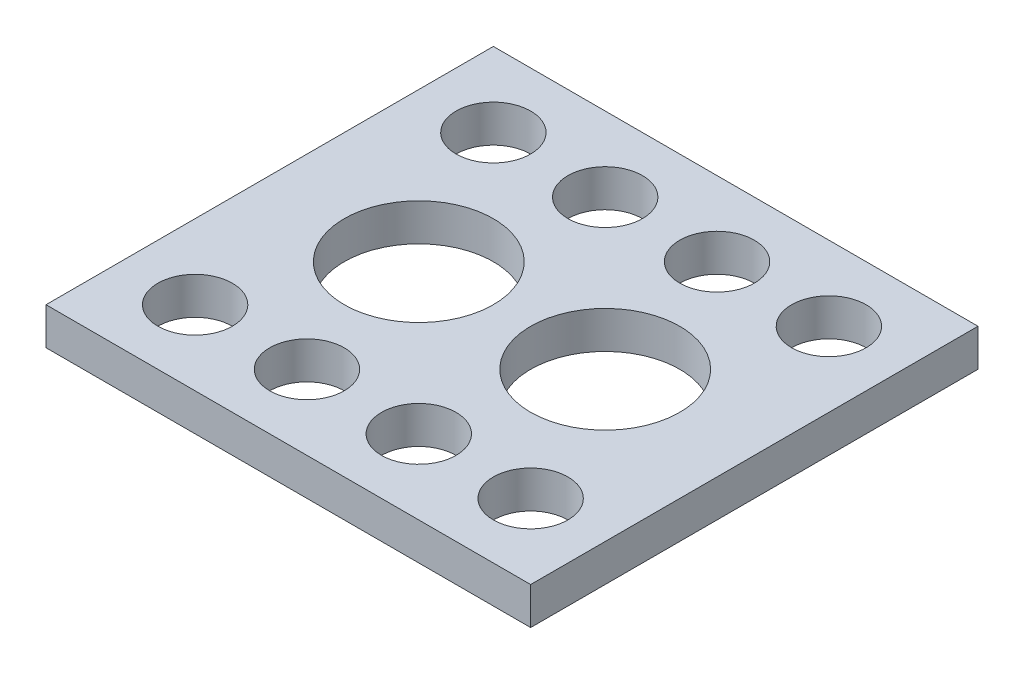
SolidWorks part; units mm, degrees
ref_plane "Front Plane" through (0, 0, 0) normal (0, 0, 1) x (1, 0, 0)
ref_plane "Top Plane" through (0, 0, 0) normal (0, 1, 0) x (1, 0, 0)
ref_plane "Right Plane" through (0, 0, 0) normal (1, 0, 0) x (0, 0, -1)
sketch "Sketch1" plane through (0, 0, 0) normal (0, 1, 0) x (1, 0, 0)
  line L1 (0, 0) -> (165.1, 0)
  line L2 (0, 0) -> (0, 152.4)
  line L3 (0, 152.4) -> (165.1, 152.4)
  line L4 (165.1, 0) -> (165.1, 152.4)
  dimension "D1" = 152.4
  dimension "D2" = 165.1
extrude "Boss-Extrude1" add sketch "Sketch1" against normal blind 12.7
sketch "Sketch2" plane through (0, 0, 0) normal (0, 1, 0) x (1, 0, 0)
  line L0 (0, 152.4) -> (0, 0) construction
  line L1 (165.1, 152.4) -> (0, 152.4) construction
  circle A0 centre (25.4, 127) radius 12.7
  circle A1 centre (63.5, 127) radius 12.7
  circle A2 centre (101.6, 127) radius 12.7
  circle A3 centre (139.7, 127) radius 12.7
  circle A4 centre (63.5, 25.4) radius 12.7
  circle A5 centre (101.6, 25.4) radius 12.7
  circle A6 centre (139.7, 25.4) radius 12.7
  circle A7 centre (25.4, 25.4) radius 12.7
  dimension "D3" = 25.4
  dimension "D1" = 25.4
  dimension "D2" = 25.4
  dimension "D6" = 38.1
  dimension "D7" = 101.6
  dimension "D8" = 25.4
  dimension "D4" = 4
  dimension "D5" = 2
extrude "Cut-Extrude1" cut sketch "Sketch2" against normal blind 12.7
sketch "Sketch3" plane through (0, 0, 0) normal (0, 1, 0) x (1, 0, 0)
  line L0 (0, 152.4) -> (0, 0) construction
  line L1 (165.1, 152.4) -> (0, 152.4) construction
  circle A0 centre (50.8, 76.2) radius 25.4
  circle A1 centre (114.3, 76.2) radius 25.4
  dimension "D2" = 50.8
  dimension "D1" = 50.8
  dimension "D3" = 76.2
  dimension "D5" = 63.5
  dimension "D4" = 2
extrude "Cut-Extrude2" cut sketch "Sketch3" against normal blind 12.7
